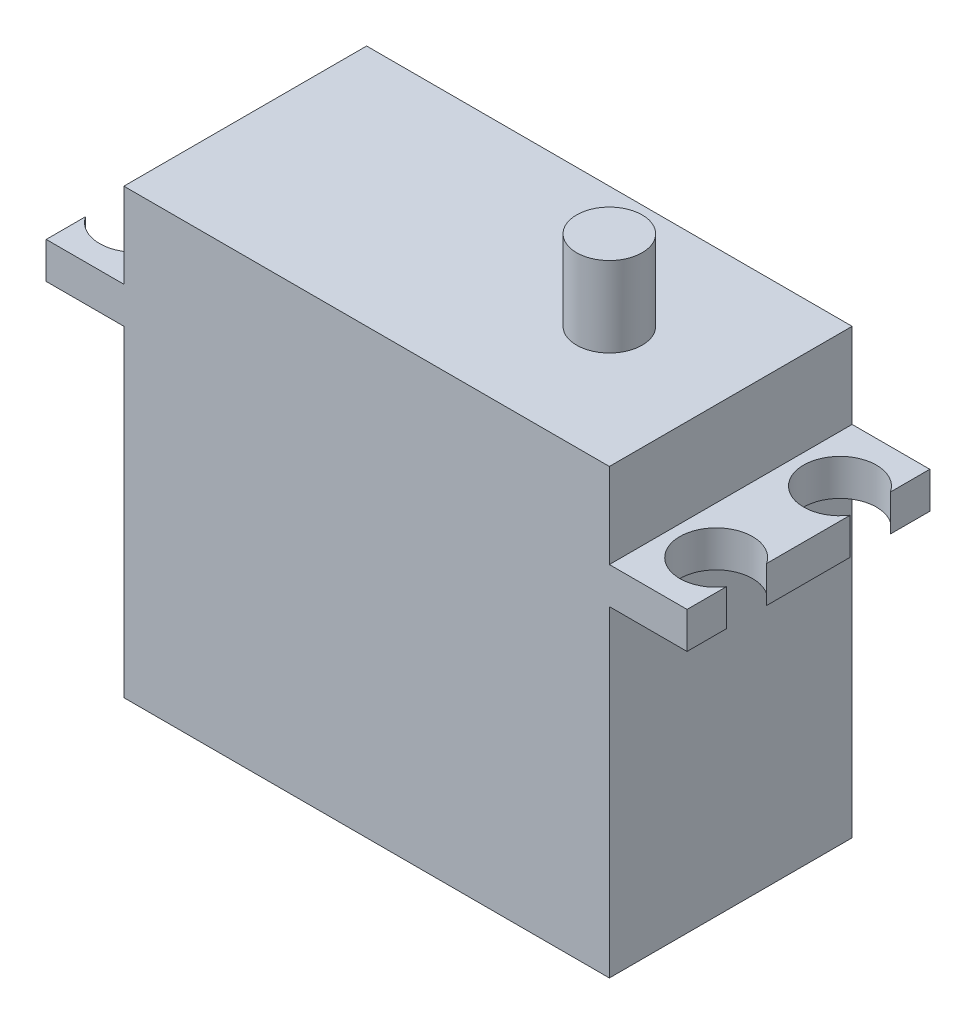
SolidWorks part; units mm, degrees
ref_plane "前基準面" through (0, 0, 0) normal (0, 0, 1) x (1, 0, 0)
ref_plane "上基準面" through (0, 0, 0) normal (0, 1, 0) x (1, 0, 0)
ref_plane "右基準面" through (0, 0, 0) normal (1, 0, 0) x (0, 0, -1)
sketch "草圖1" plane through (0, 0, 0) normal (0, 0, 1) x (1, 0, 0)
  line L0 (0, -7) -> (-6.4, -7)
  line L1 (0, 0) -> (40, 0)
  line L2 (0, 0) -> (0, -7)
  line L3 (0, -36.5) -> (40, -36.5)
  line L4 (40, 0) -> (40, -7)
  line L5 (-6.4, -7) -> (-6.4, -10)
  line L6 (-6.4, -10) -> (0, -10)
  line L7 (40, -10) -> (46.4, -10)
  line L8 (46.4, -10) -> (46.4, -7)
  line L9 (46.4, -7) -> (40, -7)
  line L10 (20, 0) -> (20, -36.5) construction
  line L11 (0, -10) -> (0, -36.5)
  line L12 (40, -10) -> (40, -36.5)
  dimension "D1" = 40
  dimension "D2" = 36.5
  dimension "D3" = 52.8
  dimension "D4" = 26.4
  dimension "D5" = 26.5
  dimension "D6" = 26.5
  dimension "D7" = 3
  dimension "D8" = 3
extrude "填料-伸長1" add sketch "草圖1" along normal blind 20
sketch "草圖2" plane through (0, -7, 0) normal (0, 1, 0) x (1, 0, 0)
  line L0 (20, 0) -> (20, -20) construction
  line L1 (40, 0) -> (0, 0) construction
  line L2 (40, -20) -> (0, -20) construction
  line L3 (-6.4, -10) -> (20, -10) construction
  line L4 (-6.4, -20) -> (-6.4, 0) construction
  circle A0 centre (-3.9, -4.9) radius 3
  circle A1 centre (-3.9, -15.1) radius 3
  circle A2 centre (43.9, -15.1) radius 3
  circle A3 centre (43.9, -4.9) radius 3
  dimension "D1" = 23.9
  dimension "D2" = 23.9
  dimension "D3" = 10.2
  dimension "D4" = 5.1
  dimension "D5" = 6
  dimension "D6" = 6
extrude "除料-伸長1" cut sketch "草圖2" against normal through all
sketch "草圖3" plane through (0, 0, 0) normal (0, 1, 0) x (1, 0, 0)
  line L0 (0, -10) -> (40, -10) construction
  line L1 (0, -20) -> (0, 0) construction
  line L2 (40, -20) -> (40, 0) construction
  line L3 (40, -20) -> (40, 0) construction
  circle A0 centre (30, -10) radius 2.7
  dimension "D1" = 10
  dimension "D2" = 5.4
extrude "填料-伸長2" add sketch "草圖3" along normal blind 6.6
sketch "草圖4" plane through (0, 6.6, 0) normal (0, 1, 0) x (1, 0, 0)
  circle A0 centre (30, -10) radius 2.6
  dimension "D1" = 5.2
extrude "填料-伸長3" [suppressed] add sketch "草圖4" against normal blind 2.5
sketch "草圖5" [suppressed] plane through (0, 6.6, 0) normal (0, 1, 0) x (1, 0, 0)
  line L0 (30, 7.5) -> (30, -10) construction
  line L1 (30, -10) -> (47.5, -10) construction
  circle A0 centre (30, -10) radius 17.5 construction
